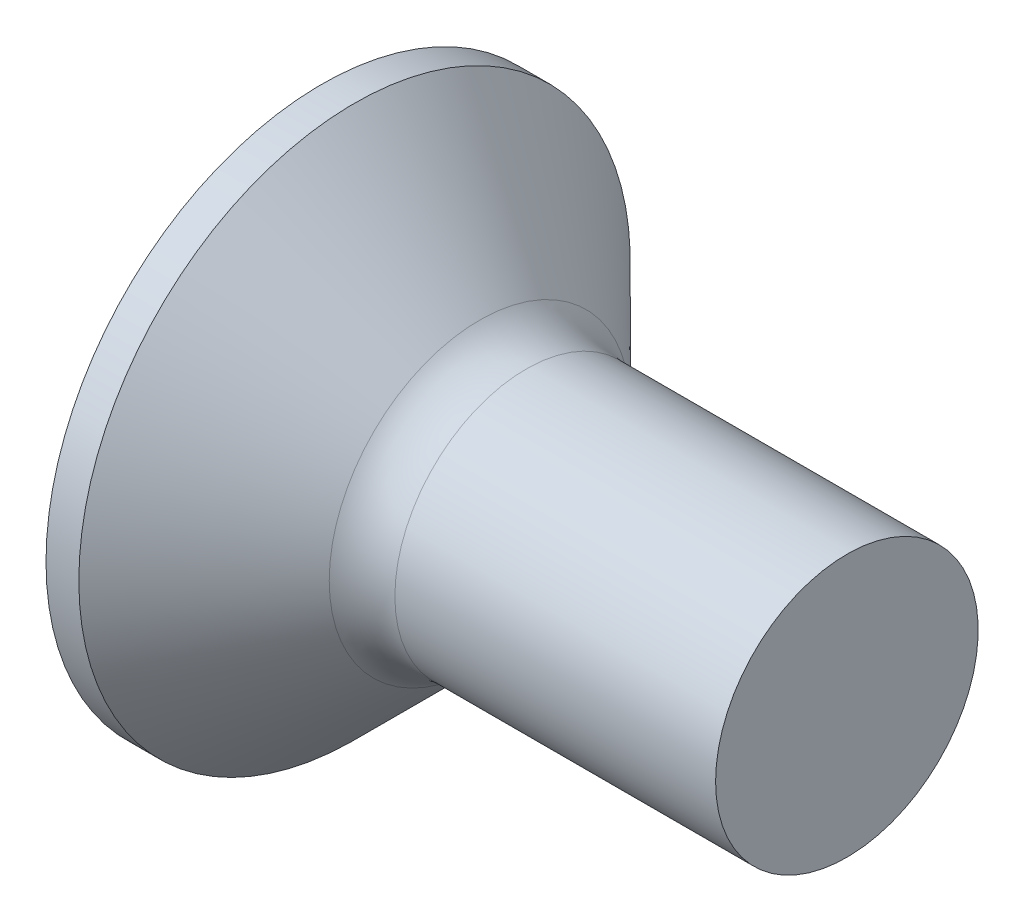
SolidWorks part; units mm, degrees
revolve "Base-Revolve" add sketch "BodySke"
sketch "BodySke" plane through (0, 0, 0) normal (0, 0, 1) x (1, 0, 0)
  line L0 (0, 0) -> (0, 4.2)
  line L1 (0, 4.2) -> (0.5, 4.2)
  line L2 (2.7, 2) -> (8, 2)
  line L3 (8, 2) -> (8, 0)
  line L4 (8, 0) -> (0, 0)
  line L5 (-6.35, 0) -> (82.55, 0) construction
  line L6 (2.7, -2) -> (8, -2) construction
  line L7 (0.5, -4.2) -> (2.7, -2) construction
  line L8 (0.5, 4.2) -> (2.7, 2)
  line L9 (0, -4.2) -> (0.5, -4.2) construction
  line L10 (3.4, 3.5875) -> (3.4, -5.9375) construction
  line L11 (0, 6.35) -> (0, -3.175) construction
  dimension "Diameter" = 4
  dimension "Length" = 8
  dimension "Head_ht" = 2.7
  dimension "Head_dia" = 8.4
  dimension "Head_ang" = 90
  dimension "D6" = 0.5
  dimension "Advance" = 0.7
  dimension "Thread_nom" = 8
cosmetic thread "ThreadCosmetic" [suppressed]
fillet "Fillet1" radius 1 1 edges at (2.7, 0, 2)
ref_plane "Plane1" through (0, 0, 0) normal (0, 0, 1) x (1, 0, 0)
ref_plane "Plane2" through (0, 0, 0) normal (0, 1, 0) x (1, 0, 0)
ref_plane "Plane3" through (0, 0, 0) normal (1, 0, 0) x (0, 0, -1)
sketch "Sketch3" plane through (0, 0, 0) normal (-1, 0, 0) x (0, 0, 1)
  line L0 (-0.515, 2.2) -> (0.515, 2.2)
  line L1 (0.515, 2.2) -> (0.515, -2.2)
  line L2 (0.515, -2.2) -> (-0.515, -2.2)
  line L3 (-0.515, -2.2) -> (-0.515, 2.2)
  dimension "Cross_dia" = 4.4
  dimension "Cross_width" = 1.03
  dimension "D1" = 2.2
  dimension "D2" = 0.515
ref_plane "Plane4" through (2.51, 0, 0) normal (-1, 0, 0) x (0, 0, 1)
sketch "Sketch4" plane through (2.51, 0, 0) normal (-1, 0, 0) x (0, 0, 1)
  line L0 (-0.515, 0.9486) -> (0.515, 0.9486)
  line L3 (0.515, 0.9486) -> (0.515, -0.9486)
  line L4 (0.515, -0.9486) -> (-0.515, -0.9486)
  line L5 (-0.515, -0.9486) -> (-0.515, 0.9486)
  dimension "D2" = 1.8971
  dimension "D1" = 1.03
  dimension "D4" = 0.9486
  dimension "D3" = 0.515
loft "Recess" cut profiles "Sketch3", "Sketch4"
pattern_circular "RecPat" count 2 every 90 about axis through (0, 0, 0) along (1, 0, 0) of "Recess"
sketch "RecCorSke" plane through (0, 0, 0) normal (0, 0, 1) x (1, 0, 0)
  line L0 (-3.175, 0) -> (15.875, 0) construction
  line L2 (0, 0) -> (0, 1.0265)
  line L3 (0, 1.0265) -> (2.51, 0.851)
  line L4 (2.51, 0.851) -> (2.7865, 0)
  line L5 (2.7865, 0) -> (0, 0)
  dimension "Diameter" = 1.702
  dimension "Depth" = 2.51
  dimension "Draft_angle" = 4
  dimension "Bottom_angle" = 18
revolve "RecessCore" cut sketch "RecCorSke" angle 360 about L0
sketch "ThdSchSke" plane through (0, 0, 0) normal (0, 0, 1) x (1, 0, 0)
  line L0 (3.4, -1.61) -> (3.1269, -2)
  line L1 (3.4, -1.61) -> (3.6731, -2)
  line L2 (3.6731, -2) -> (3.6731, -2.5)
  line L3 (-3.175, 0) -> (5.1513, 0) construction
  line L5 (3.6731, -2.5) -> (3.1269, -2.5)
  line L6 (3.1269, -2.5) -> (3.1269, -2)
  line L7 (0, 4.2) -> (0, -4.2) construction
  dimension "Diameter" = 4
  dimension "Thread_minor" = 3.22
  dimension "Start" = 3.4
revolve "ThreadSchematic" [suppressed] cut sketch "ThdSchSke" angle 360 about L3
pattern_linear "ThdSchPat" [suppressed]
equation "\"D1@Sketch3\" = \"Cross_dia@Sketch3\" / 2"
equation "\"D2@Sketch3\" = \"Cross_width@Sketch3\" / 2"
equation "\"Depth@RecCorSke\" = \"Cross_depth@Plane4\""
equation "\"D1@Sketch4\" = \"Cross_width@Sketch3\""
equation "\"D2@Sketch4\" = \"Cross_dia@Sketch3\" - 2.0 * \"Cross_depth@Plane4\" * tan(26.5  * 0.017453292)"
equation "\"D3@Sketch4\" = \"D1@Sketch4\" / 2"
equation "\"D4@Sketch4\" = \"D2@Sketch4\" / 2"
equation "\"Thread_length@ThreadCosmetic\" = ((sgn( (\"Length@BodySke\" - \"Advance@BodySke\" * 1.0 - \"Head_ht@BodySke\" ) - \"Thread_nom@BodySke\" )-1)*( (\"Length@BodySke\" - \"Advance@BodySke\" * 1.0 - \"Head_ht@BodySke\" ) - \"Thread_nom@BodySke\" ))/-2+ \"Thread_nom@BodySke\""
equation "\"Thread_minor@ThdSchSke\" = \"Thread_minor@ThreadCosmetic\""
equation "\"Diameter@ThdSchSke\" = \"Diameter@BodySke\""
equation "\"Overcut@ThdSchSke\" = \"Diameter@BodySke\" * 1.25"
equation "\"Start@ThdSchSke\" = 0.000001 + \"Length@BodySke\" - \"Thread_length@ThreadCosmetic\"  '---Countersunk---"
equation "\"Num_threads@ThdSchPat\" = int( \"Thread_length@ThreadCosmetic\" / \"Advance@BodySke\" + 0.999 )  + 1"
equation "\"Advance@ThdSchPat\" = \"Thread_length@ThreadCosmetic\" /  (\"Num_threads@ThdSchPat\" - 1) 'relax it"
